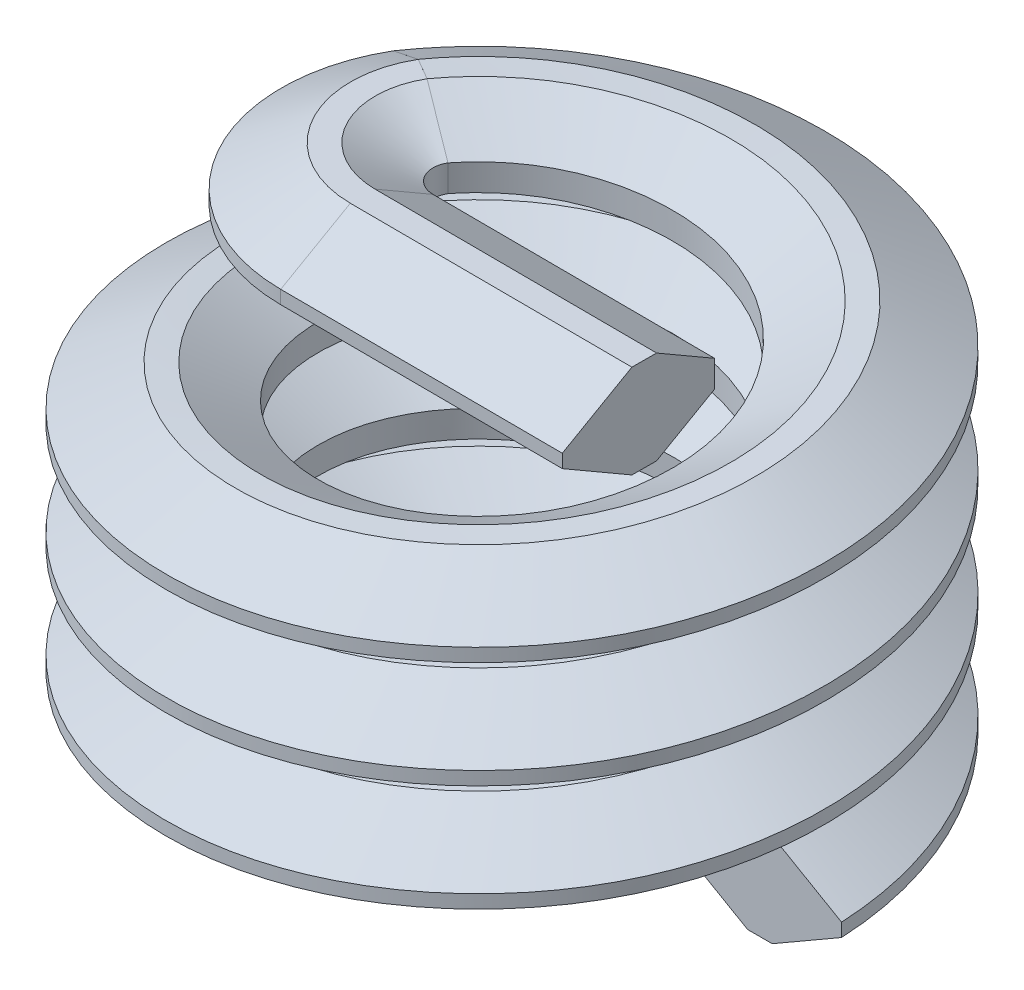
SolidWorks part; units mm, degrees
ref_plane "Front Plane" through (0, 0, 0) normal (0, 0, 1) x (1, 0, 0)
ref_plane "Top Plane" through (0, 0, 0) normal (0, 1, 0) x (1, 0, 0)
ref_plane "Right Plane" through (0, 0, 0) normal (1, 0, 0) x (0, 0, -1)
sketch "Sketch1" plane through (0, 0, 0) normal (0, 0, 1) x (-1, 0, 0)
  line L0 (0, 0) -> (0, 9.525) construction
  line L1 (-1.1511, 0) -> (-1.8385, 0.3969) construction
  line L2 (-1.8496, 0.3969) -> (-2.537, 0) construction
  line L3 (-2.537, 0) -> (-1.8496, -0.3969) construction
  line L4 (-1.8385, -0.3969) -> (-1.1511, 0) construction
  line L5 (-1.8385, -0.3969) -> (-1.8385, 0.3969) construction
  line L6 (-1.1511, 0) -> (0, 0) construction
  line L8 (-2.4511, -0.0496) -> (-1.9355, -0.3473)
  line L9 (-1.7526, -0.3473) -> (-1.323, -0.0992)
  line L10 (-1.237, -0.0496) -> (-1.237, 0.0496) construction
  line L11 (-1.323, 0.0992) -> (-1.7526, 0.3473)
  line L12 (-1.9355, 0.3473) -> (-2.4511, 0.0496)
  line L13 (-1.1511, 0) -> (-1.237, 0) construction
  line L14 (-1.237, 0) -> (-1.7526, 0) construction
  line L15 (-1.9355, 0) -> (-2.4511, 0) construction
  line L16 (-2.4511, 0) -> (-2.537, 0) construction
  line L17 (-1.9355, 0.3473) -> (-1.7526, 0.3473)
  line L18 (-1.7526, 0.3473) -> (-1.7526, -0.3473) construction
  line L19 (-1.7526, -0.3473) -> (-1.9355, -0.3473)
  line L20 (-1.9355, -0.3473) -> (-1.9355, 0.3473) construction
  line L21 (-1.9355, 0) -> (-1.8385, 0) construction
  line L22 (-1.8385, 0) -> (-1.7526, 0) construction
  line L23 (-2.4511, 0.3969) -> (-2.4511, -3.1083) construction
  line L24 (-1.323, -0.0992) -> (-1.323, 0.0992)
  line L25 (-1.323, 0) -> (-1.237, 0) construction
  line L26 (-2.4511, -0.0496) -> (-2.4511, 0.0496)
  line L28 (2.4511, 0.3969) -> (2.4511, -3.1083) construction
  line L29 (-1.8385, -0.3969) -> (-1.8496, -0.3969) construction
  line L31 (-1.8496, 0.3969) -> (-1.8385, 0.3969) construction
  dimension "D3" = 0.7937
  dimension "D4" = 0.0992
  dimension "Installed Length" = 3.5052
  dimension "Thread Size" = 3.5052
  dimension "Max OD" = 4.9022
sketch "Sketch2" plane through (0, 0, 0) normal (0, 1, 0) x (1, 0, 0)
  circle A0 centre (0, 0) radius 1.7526
curve "Helix/Spiral1" pitch 0.7937 height 2.7115 turns 3.416 parameters "Height"=2.7115, "Pitch"=0.7937
sweep "Sweep1" add profiles "Sketch1" path "Helix/Spiral1"
sketch "Sketch3" plane through (0, 0, 0) normal (-0.5036, 0, 0.8639) x (0.8639, 0, 0.5036)
  line L0 (-5.134, 0.4115) -> (-1.1511, 2.7111) construction
  line L1 (-8.8354, 7.1475) -> (-1.1511, 2.7111) construction
  line L2 (-1.1511, 2.7111) -> (-1.1511, 2.9095) construction
  line L8 (-1.7526, 2.3638) -> (-1.323, 2.6118)
  line L9 (-1.323, 2.6118) -> (-1.323, 2.8103)
  line L10 (-1.323, 2.8103) -> (-1.7526, 3.0583)
  line L12 (-1.9355, 3.0583) -> (-2.4511, 2.7607)
  line L13 (-2.4511, 2.7607) -> (-2.4511, 2.6614)
  line L14 (-2.4511, 2.6614) -> (-1.9355, 2.3638)
  line L16 (-1.7526, 2.3638) -> (-1.323, 2.6118)
  line L17 (-1.323, 2.6118) -> (-1.323, 2.8103)
  line L18 (-1.323, 2.8103) -> (-1.7526, 3.0583)
  line L20 (-1.9355, 3.0583) -> (-2.4511, 2.7607)
  line L21 (-2.4511, 2.7607) -> (-2.4511, 2.6614)
  line L22 (-2.4511, 2.6614) -> (-1.9355, 2.3638)
  line L23 (-1.7526, 3.0583) -> (-1.9355, 3.0583)
  line L24 (-1.7526, 3.0583) -> (-1.9355, 3.0583)
  line L25 (-1.9355, 2.3638) -> (-1.7526, 2.3638)
  line L26 (-1.9355, 2.3638) -> (-1.7526, 2.3638)
  dimension "D1" = 0
revolve "Revolve1" add sketch "Sketch3" angle 120 about L2
sketch "Sketch4" plane through (-0.9969, 0, -0.0041) normal (1, 0, 0.0042) x (0.0042, 0, -1)
  line L8 (-0.2089, 2.3638) -> (-0.0259, 2.3638)
  line L9 (-0.0259, 2.3638) -> (0.4037, 2.6118)
  line L10 (0.4037, 2.6118) -> (0.4037, 2.8103)
  line L11 (0.4037, 2.8103) -> (-0.0259, 3.0583)
  line L12 (-0.2089, 2.3638) -> (-0.0259, 2.3638)
  line L13 (-0.2089, 3.0583) -> (-0.7244, 2.7607)
  line L14 (-0.7244, 2.7607) -> (-0.7244, 2.6614)
  line L15 (-0.7244, 2.6614) -> (-0.2089, 2.3638)
  line L17 (-0.0259, 2.3638) -> (0.4037, 2.6118)
  line L18 (0.4037, 2.6118) -> (0.4037, 2.8103)
  line L19 (0.4037, 2.8103) -> (-0.0259, 3.0583)
  line L21 (-0.2089, 3.0583) -> (-0.7244, 2.7607)
  line L22 (-0.7244, 2.7607) -> (-0.7244, 2.6614)
  line L23 (-0.7244, 2.6614) -> (-0.2089, 2.3638)
  spline S4 degree 1 poles (1999.9718, 3.0654) (-2000.2019, 3.0512) knots -10932.279875 -10932.279875 10933.254144 10933.254144 only from (-0.0259, 3.0583) to (-0.2089, 3.0583)
  spline S5 degree 1 poles (-0.0259, 3.0583) (-0.2089, 3.0583) knots 0 0 1 1
  dimension "D1" = 0
extrude "Extrude1" add sketch "Sketch4" along normal blind 2.1031
sketch "Sketch5" plane through (0, 0, 0) normal (0, 1, 0) x (1, 0, 0)
  circle A0 centre (0, 0) radius 2.9538
equation "\"D3@Sketch1\" = \"Pitch@Helix/Spiral1\""
equation "\"D4@Sketch1\" = \"D3@Sketch1\"  * 1 / 8"
equation "\"D1@Extrude1\" = \"Thread Size@Sketch1\" * 0.6"
equation "\"Height@Helix/Spiral1\" = \"Installed Length@Sketch1\" - \"Pitch@Helix/Spiral1\""
